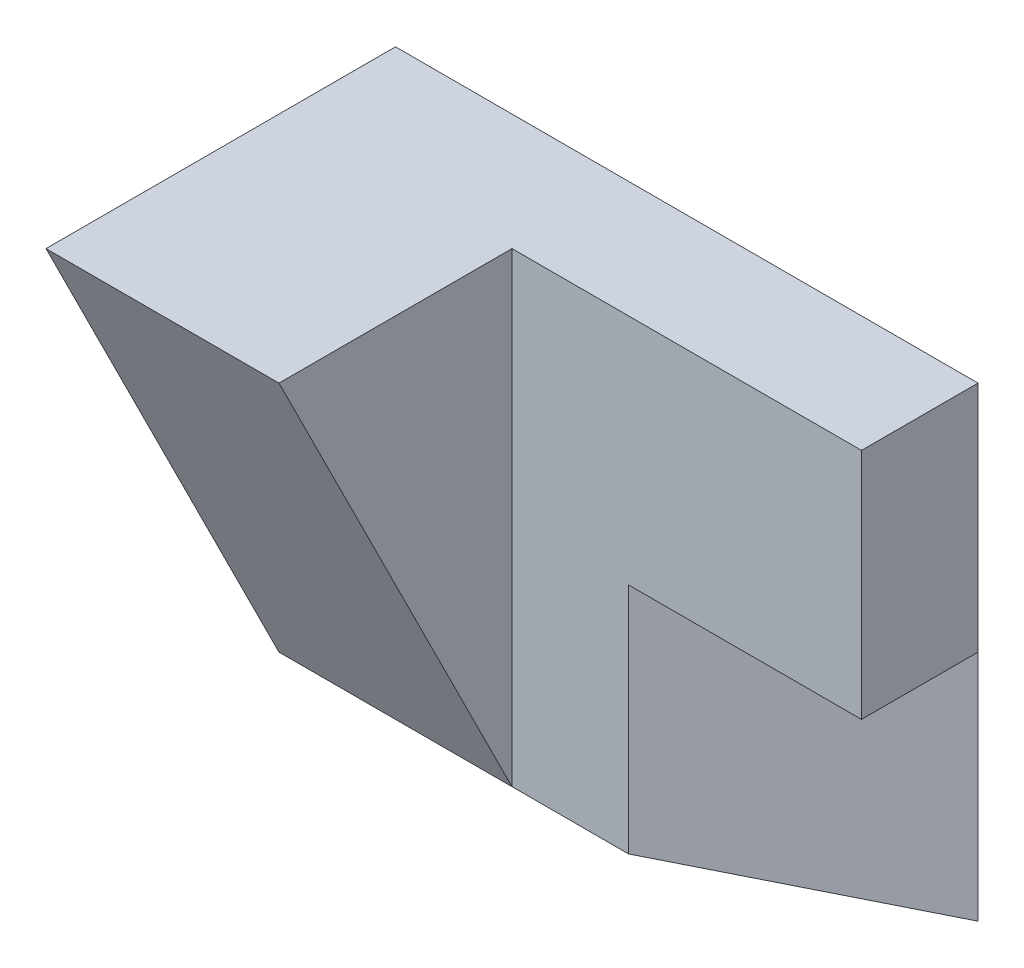
SolidWorks part; units mm, degrees
ref_plane "Front Plane" through (0, 0, 0) normal (0, 0, 1) x (1, 0, 0)
ref_plane "Top Plane" through (0, 0, 0) normal (0, 1, 0) x (1, 0, 0)
ref_plane "Right Plane" through (0, 0, 0) normal (1, 0, 0) x (0, 0, -1)
sketch "Sketch1" plane through (0, 0, 0) normal (0, 0, 1) x (1, 0, 0)
  line L1 (0, 0) -> (50, 0)
  line L2 (0, 0) -> (0, 40)
  line L3 (0, 40) -> (50, 40)
  line L4 (50, 0) -> (50, 40)
  dimension "D1" = 50
  dimension "D2" = 40
extrude "Boss-Extrude1" add sketch "Sketch1" along normal blind 10
sketch "Sketch3" plane through (0, 0, 0) normal (0, -1, 0) x (1, 0, 0)
  line L2 (0, 10) -> (50, 10) construction
  line L3 (30, 10) -> (50, 0)
  line L5 (30, 10) -> (50, 10)
  line L6 (50, 10) -> (50, 0)
  dimension "D1" = 20
extrude "Cut-Extrude1" cut sketch "Sketch3" against normal blind 20
sketch "Sketch4" plane through (0, 0, 10) normal (0, 0, 1) x (1, 0, 0)
  line L0 (0, 40) -> (0, 0) construction
  line L1 (0, 40) -> (20, 40)
  line L2 (0, 40) -> (0, 0)
  line L3 (0, 0) -> (20, 0)
  line L4 (20, 40) -> (20, 0)
  line L5 (0, 0) -> (30, 0) construction
  dimension "D1" = 20
extrude "Boss-Extrude3" add sketch "Sketch4" along normal blind 20
sketch "Sketch7" plane through (0, 0, 0) normal (-1, 0, 0) x (0, 0, 1)
  line L3 (30, 40) -> (10, 0)
  line L4 (30, 0) -> (0, 0) construction
  line L5 (10, 0) -> (30, 0)
  line L6 (30, 0) -> (30, 40)
  dimension "D1" = 40
  dimension "D2" = 10
extrude "Cut-Extrude3" cut sketch "Sketch7" against normal blind 20
